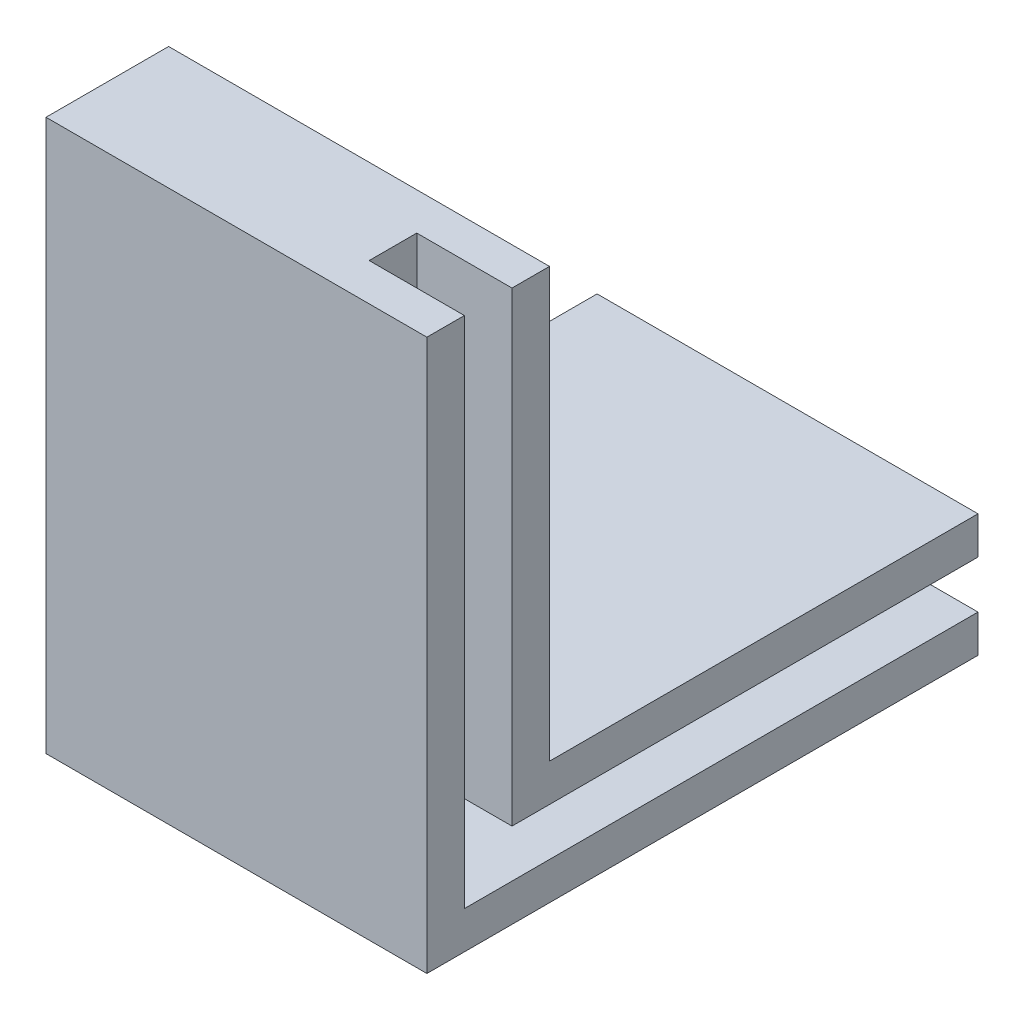
SolidWorks part; units mm, degrees
material "ABS"
ref_plane "Front Plane" through (0, 0, 0) normal (0, 0, 1) x (1, 0, 0)
ref_plane "Top Plane" through (0, 0, 0) normal (0, 1, 0) x (1, 0, 0)
ref_plane "Right Plane" through (0, 0, 0) normal (1, 0, 0) x (0, 0, -1)
sketch "Sketch2" plane through (0, 0, 0) normal (1, 0, 0) x (0, 0, -1)
  line L0 (0, 0) -> (73.5, 0)
  line L1 (73.5, 0) -> (73.5, 16.35)
  line L2 (73.5, 16.35) -> (16.35, 16.35)
  line L3 (16.35, 16.35) -> (16.35, 73.5)
  line L4 (16.35, 73.5) -> (0, 73.5)
  line L5 (0, 73.5) -> (0, 0)
  point P6 (0, 0)
  point P8 (4.124, 3.6214)
  point P9 (0, 0)
  point P10 (0, 0)
  dimension "D1" = 16.35
  dimension "D2" = 16.35
  dimension "D3" = 73.5
  dimension "D4" = 73.5
extrude "Boss-Extrude2" add sketch "Sketch2" along normal blind 50.8
sketch "Sketch3" plane through (50.8, 0, 0) normal (1, 0, 0) x (0, 0, -1)
  line L0 (5, 5) -> (73.5, 5)
  line L1 (73.5, 0) -> (73.5, 16.35) construction
  line L2 (73.5, 5) -> (73.5, 11.35)
  line L3 (73.5, 11.35) -> (11.35, 11.35)
  line L4 (11.35, 11.35) -> (11.35, 73.5)
  line L5 (16.35, 73.5) -> (0, 73.5) construction
  line L6 (11.35, 73.5) -> (5, 73.5)
  line L7 (5, 73.5) -> (5, 5)
  line L8 (0, 0) -> (73.5, 0) construction
  line L9 (73.5, 16.35) -> (16.35, 16.35) construction
  line L10 (16.35, 16.35) -> (16.35, 73.5) construction
  line L11 (0, 73.5) -> (0, 0) construction
  dimension "D1" = 5
  dimension "D2" = 5
  dimension "D3" = 5
  dimension "D4" = 5
extrude "Cut-Extrude1" cut sketch "Sketch3" against normal blind 12.7
equation "\"D1@Boss-Extrude1\"=1.5in"
equation "\"D1@Sketch2\"=5*2+.25in"
equation "\"D2@Sketch2\"=\"D1@Sketch2\""
equation "\"D1@Boss-Extrude2\"=1.5in+.5in"
equation "\"D1@Cut-Extrude1\"=.5in"
equation "\"D4@Sketch2\"=\"D3@Sketch2\""
